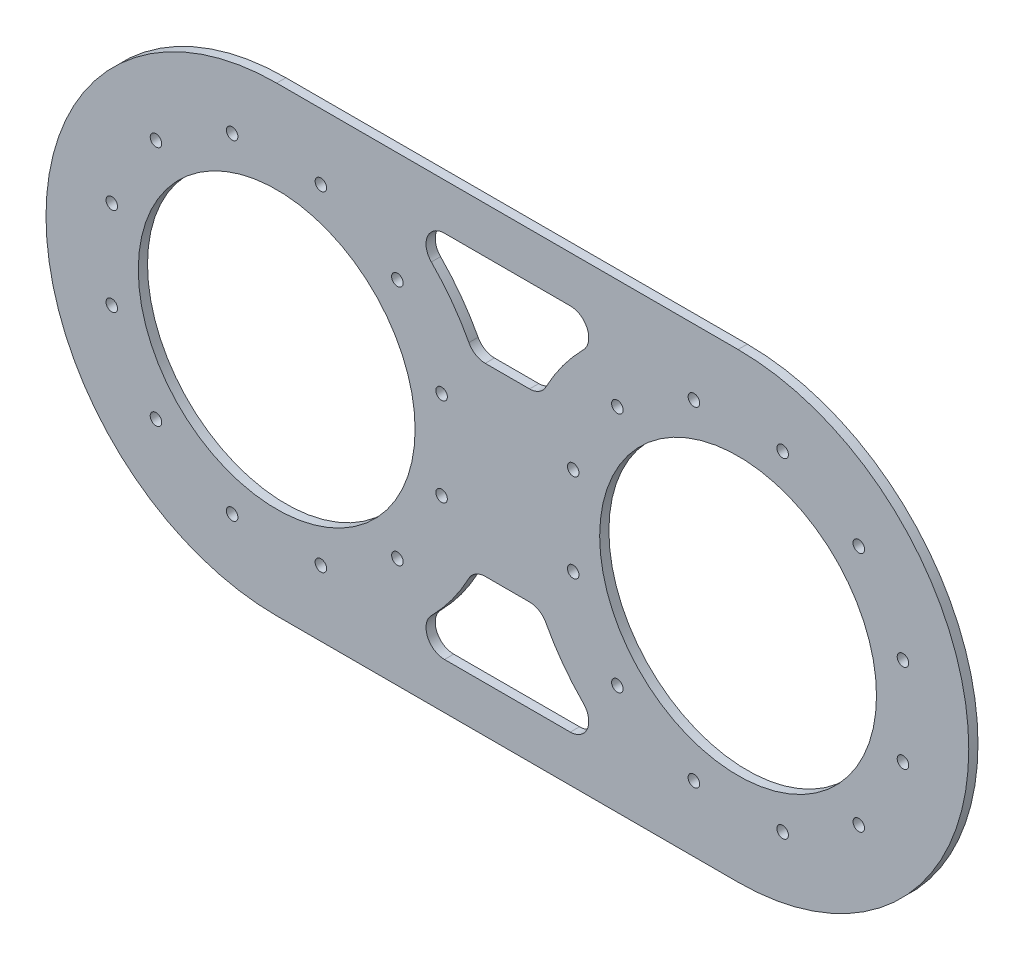
SolidWorks part; units mm, degrees
ref_plane "前视基准面" through (0, 0, 0) normal (0, 0, 1) x (1, 0, 0)
ref_plane "上视基准面" through (0, 0, 0) normal (0, 1, 0) x (1, 0, 0)
ref_plane "右视基准面" through (0, 0, 0) normal (1, 0, 0) x (0, 0, -1)
sketch "草图1" plane through (0, 0, 0) normal (0, 0, 1) x (1, 0, 0)
  line L5 (55, 0) -> (-55, 0) construction
  line L9 (-7.28, -20) -> (7.28, -20)
  line L11 (-50, 50) -> (-25, 50)
  line L12 (25, 40) -> (-25, 40)
  line L13 (-7.28, 20) -> (7.28, 20)
  line L14 (25, -40) -> (-25, -40)
  line L17 (-50, -50) -> (-25, -50)
  line L18 (0, -55) -> (0, 55) construction
  line L19 (50, -50) -> (25, -50)
  line L22 (50, 50) -> (25, 50)
  line L23 (-25, -50) -> (25, -50)
  line L24 (-25, 50) -> (25, 50)
  arc A2 (50, 50) -> (50, -50) centre (50, 0) cw
  arc A3 (-50, 50) -> (-50, -50) centre (-50, 0) ccw
  circle A4 centre (-50, 0) radius 30
  circle A5 centre (50, 0) radius 30
  arc A12 (-25, 40) -> (-7.28, 20) centre (-50, 0) cw
  arc A13 (-25, -40) -> (-7.28, -20) centre (-50, 0) ccw
  arc A14 (25, -40) -> (7.28, -20) centre (50, 0) cw
  arc A15 (25, 40) -> (7.28, 20) centre (50, 0) ccw
  point P29 (0, -45)
  point P30 (0, -40)
  point P31 (0, -20)
  point P32 (0, 20)
  point P33 (0, 40)
  point P34 (0, 45)
extrude "凸台-拉伸1" add sketch "草图1" along normal blind 2
hole_wizard "M3 螺纹孔的螺纹孔钻头1" positions "3D草图1" profile "草图2" hole size "M3" standard "ISO" end condition through all
sketch3d "3D草图1"
  point P182 (-40.4237, 35.7393, 2)
  point P184 (-23.837, 26.163, 2)
  point P186 (-14.2607, 9.5763, 2)
  point P211 (-59.6568, 35.7176, 2)
  point P213 (-76.163, 26.163, 2)
  point P215 (-85.7393, 9.5763, 2)
  point P220 (85.7393, 9.5763, 2)
  point P221 (76.163, 26.163, 2)
  point P222 (59.6568, 35.7176, 2)
  point P223 (14.2607, 9.5763, 2)
  point P224 (23.837, 26.163, 2)
  point P225 (40.4237, 35.7393, 2)
  point P226 (40.4237, -35.7393, 2)
  point P227 (23.837, -26.163, 2)
  point P228 (14.2607, -9.5763, 2)
  point P229 (59.6568, -35.7176, 2)
  point P230 (76.163, -26.163, 2)
  point P231 (85.7393, -9.5763, 2)
  point P232 (-85.7393, -9.5763, 2)
  point P233 (-76.163, -26.163, 2)
  point P234 (-59.6568, -35.7176, 2)
  point P235 (-14.2607, -9.5763, 2)
  point P236 (-23.837, -26.163, 2)
  point P237 (-40.4237, -35.7393, 2)
sketch "草图2" plane through (-40.4237, 35.7393, 2) normal (1, 0, 0) x (0, -1, 0)
  line L0 (0, 0) -> (0, 2)
  line L1 (0, 2) -> (1.25, 2)
  line L2 (1.25, 2) -> (1.25, 0)
  line L5 (1.25, 0) -> (0, 0)
  line L11 (0, -6.35) -> (0, 107.95) construction
  dimension "通孔孔直径" = 2.5
  dimension "通孔孔深度" = 2
fillet "圆角1" radius 4 8 edges at (7.28, 20, 1) (-7.28, 20, 1) (25, 40, 1) (-25, 40, 1) (-7.28, -20, 1) (7.28, -20, 1) (25, -40, 1) (-25, -40, 1)
